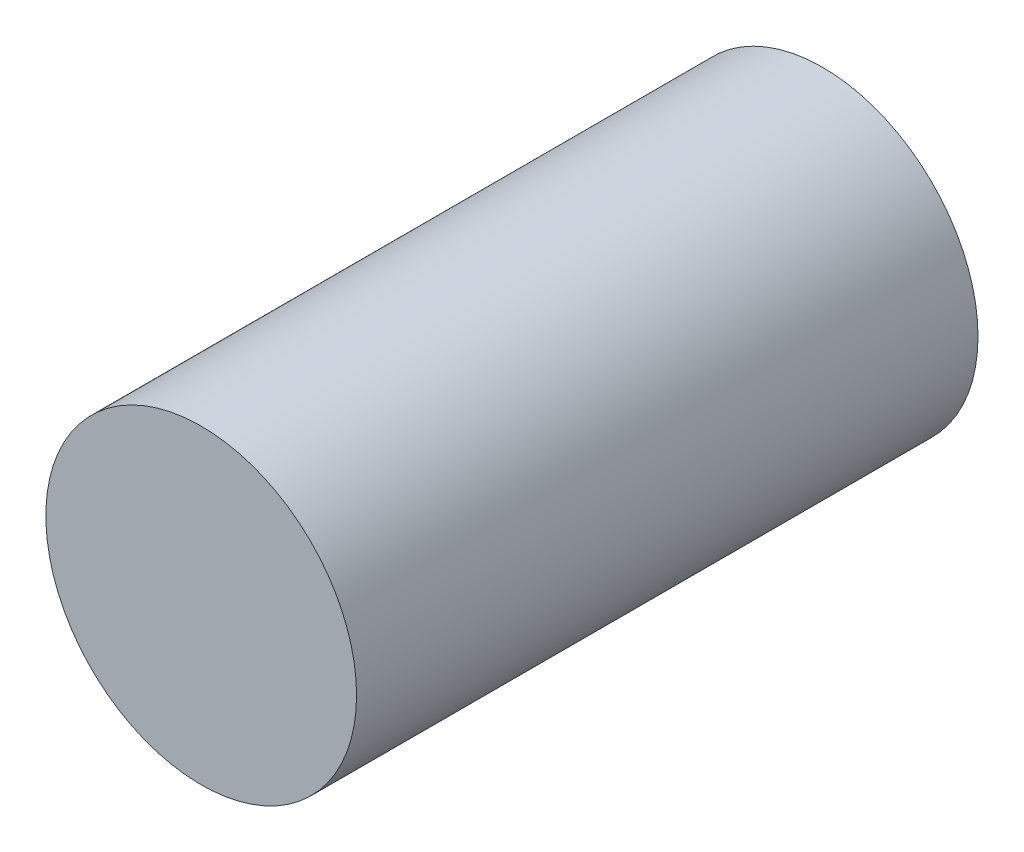
SolidWorks part; units mm, degrees
ref_plane "Front Plane" through (0, 0, 0) normal (0, 0, 1) x (1, 0, 0)
ref_plane "Top Plane" through (0, 0, 0) normal (0, 1, 0) x (1, 0, 0)
ref_plane "Right Plane" through (0, 0, 0) normal (1, 0, 0) x (0, 0, -1)
sketch "Sketch1" plane through (0, 0, 0) normal (0, 0, 1) x (1, 0, 0)
  circle A0 centre (0, 0) radius 1.5
  dimension "D1" = 3
extrude "Boss-Extrude1" add sketch "Sketch1" along normal blind 6
